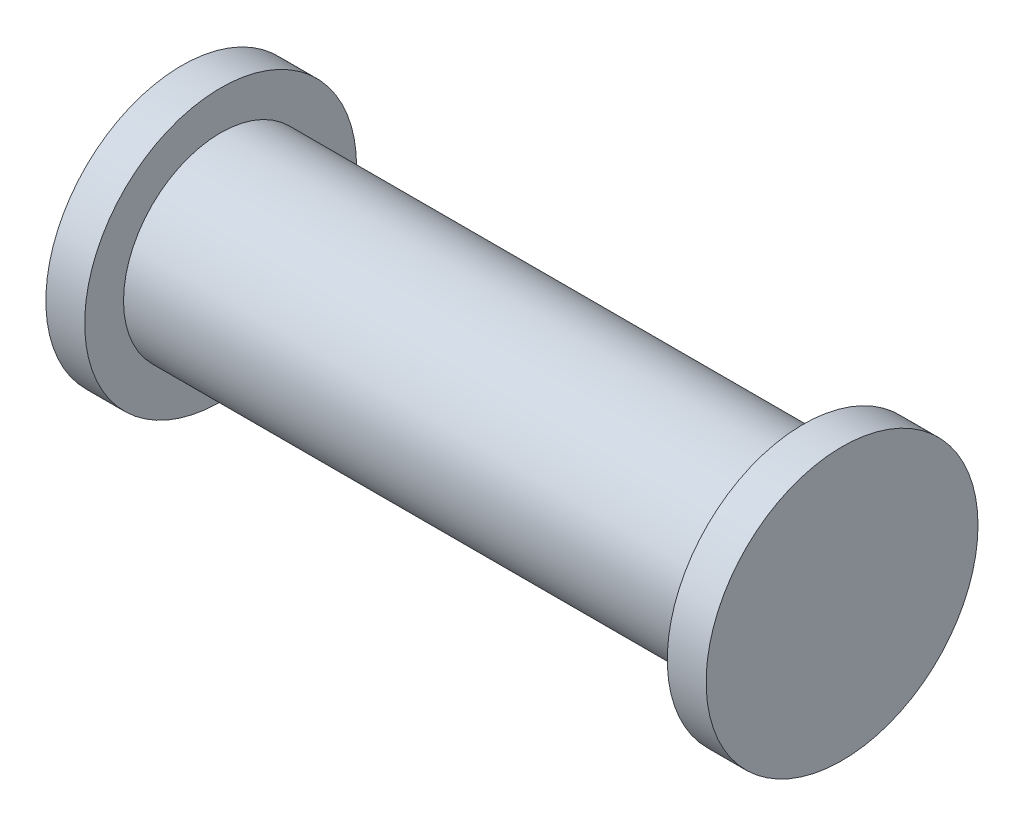
SolidWorks part; units mm, degrees
ref_plane "Front Plane" through (0, 0, 0) normal (0, 0, 1) x (1, 0, 0)
ref_plane "Top Plane" through (0, 0, 0) normal (0, 1, 0) x (1, 0, 0)
ref_plane "Right Plane" through (0, 0, 0) normal (1, 0, 0) x (0, 0, -1)
sketch "Sketch1" plane through (0, 0, 0) normal (1, 0, 0) x (0, 0, -1)
  circle A0 centre (0, 0) radius 12.5
  dimension "D1" = 25
extrude "Boss-Extrude1" add sketch "Sketch1" along normal mid plane 75
sketch "Sketch4" plane through (37.5, 0, 0) normal (1, 0, 0) x (0, 0, -1)
  circle A0 centre (0, 0) radius 17.5
  dimension "D1" = 35
extrude "Boss-Extrude3" add sketch "Sketch4" along normal blind 5
mirror "Mirror1" about plane through (0, 0, 0) normal (1, 0, 0) of "Boss-Extrude3"
